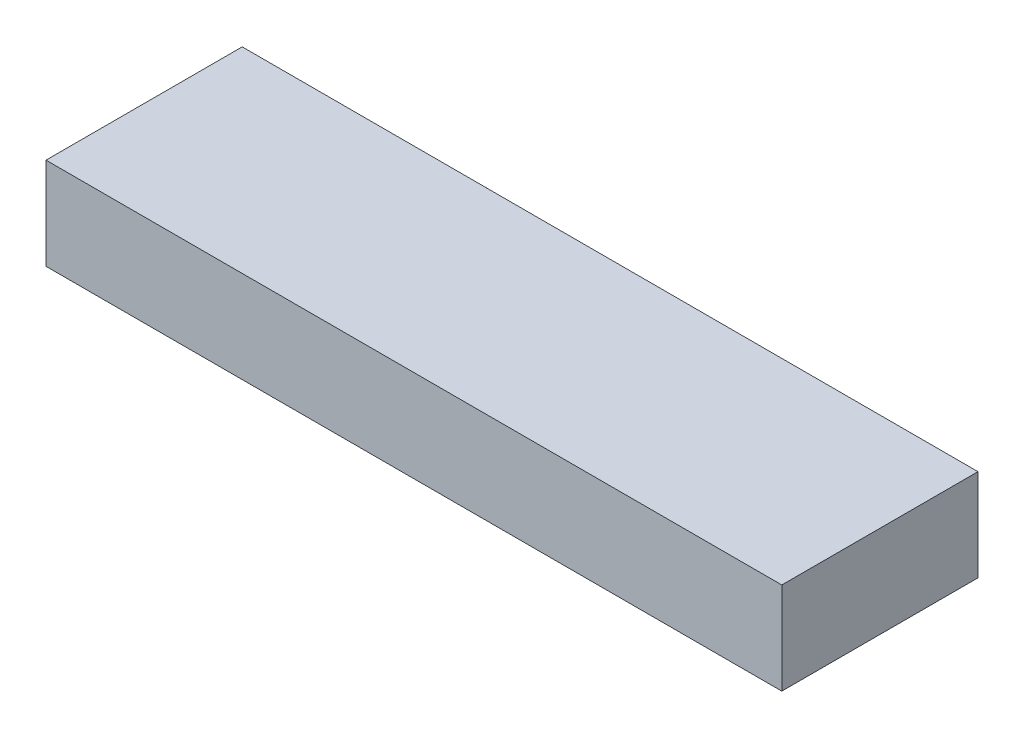
SolidWorks part; units mm, degrees
ref_plane "Front Plane" through (0, 0, 0) normal (0, 0, 1) x (1, 0, 0)
ref_plane "Top Plane" through (0, 0, 0) normal (0, 1, 0) x (1, 0, 0)
ref_plane "Right Plane" through (0, 0, 0) normal (1, 0, 0) x (0, 0, -1)
sketch "Sketch1" plane through (0, 0, 0) normal (0, 1, 0) x (1, 0, 0)
  line L1 (0, 0) -> (38.1, 0)
  line L2 (0, 0) -> (0, 10.16)
  line L3 (0, 10.16) -> (38.1, 10.16)
  line L4 (38.1, 0) -> (38.1, 10.16)
  dimension "D1" = 38.1
  dimension "D2" = 10.16
extrude "Boss-Extrude1" add sketch "Sketch1" along normal blind 4.7625
